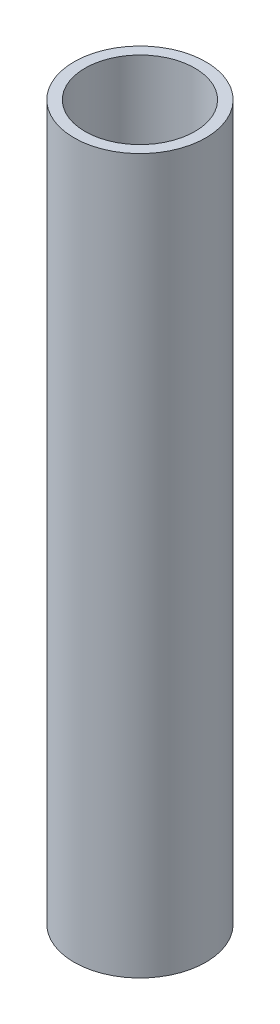
SolidWorks part; units mm, degrees
material "Aluminum Bronze"
ref_plane "Front Plane" through (0, 0, 0) normal (0, 0, 1) x (1, 0, 0)
ref_plane "Top Plane" through (0, 0, 0) normal (0, 1, 0) x (1, 0, 0)
ref_plane "Right Plane" through (0, 0, 0) normal (1, 0, 0) x (0, 0, -1)
sketch "Sketch1" plane through (0, 0, 0) normal (0, 1, 0) x (1, 0, 0)
  circle A0 centre (0, 0) radius 2.5
  circle A1 centre (0, 0) radius 3
extrude "Boss-Extrude1" add sketch "Sketch1" along normal blind 32.5
